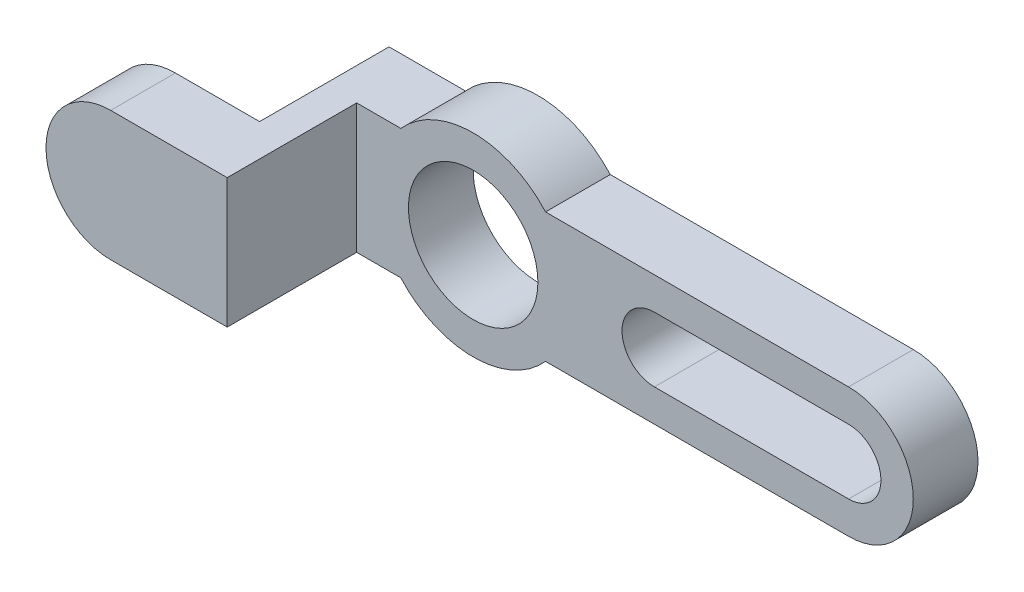
SolidWorks part; units mm, degrees
ref_plane "Front Plane" through (0, 0, 0) normal (0, 0, 1) x (1, 0, 0)
ref_plane "Top Plane" through (0, 0, 0) normal (0, 1, 0) x (1, 0, 0)
ref_plane "Right Plane" through (0, 0, 0) normal (1, 0, 0) x (0, 0, -1)
sketch "Sketch1" plane through (0, 0, 0) normal (0, 0, 1) x (1, 0, 0)
  line L0 (7.0995, 6.35) -> (31.75, 6.35)
  line L1 (-31.75, 6.35) -> (-7.0995, 6.35) construction
  line L2 (-31.75, 6.35) -> (-31.75, -6.35) construction
  line L3 (-31.75, -6.35) -> (-7.0995, -6.35) construction
  line L4 (31.75, 6.35) -> (31.75, -6.35) construction
  line L5 (-31.75, 6.35) -> (31.75, -6.35) construction
  line L6 (-31.75, -6.35) -> (31.75, 6.35) construction
  line L10 (7.0995, -6.35) -> (31.75, -6.35)
  line L14 (-17.78, 6.35) -> (-17.78, -6.35)
  line L15 (-17.78, 6.35) -> (-7.0995, 6.35)
  line L16 (-17.78, -6.35) -> (-7.0995, -6.35)
  line L17 (36.83, 6.35) -> (36.83, -6.35)
  line L18 (31.75, 6.35) -> (36.83, 6.35)
  line L19 (36.83, -6.35) -> (31.75, -6.35)
  arc A1 (-7.0995, -6.35) -> (7.0995, -6.35) centre (0, 0) ccw
  arc A5 (7.0995, 6.35) -> (-7.0995, 6.35) centre (0, 0) ccw
  circle A6 centre (0, 0) radius 6.35
  dimension "D3" = 19.05
  dimension "D4" = 12.7
  dimension "D1" = 63.5
  dimension "D2" = 12.7
  dimension "D5" = 13.97
  dimension "D6" = 36.83
extrude "Boss-Extrude1" add sketch "Sketch1" along normal mid plane 6.35
sketch "Sketch2" plane through (0, 0, -3.175) normal (0, 0, -1) x (-1, 0, 0)
  line L1 (-36.83, -6.35) -> (-36.83, 6.35) construction
  circle A0 centre (-36.83, 0) radius 6.35
  circle A1 centre (-36.83, 0) radius 3.175
  point P5 (-36.83, 0)
  dimension "D1" = 6.35
  dimension "D2" = 3.175
extrude "Boss-Extrude2" add sketch "Sketch2" against normal up to surface (6.35 mm away) up to face at (4.7625, 0, 3.175)
sketch "Sketch4" plane through (0, 0, 3.175) normal (0, 0, 1) x (1, 0, 0)
  line L1 (36.83, 3.175) -> (17.78, 3.175)
  line L2 (36.83, -3.175) -> (17.78, -3.175)
  arc A1 (36.83, -3.175) -> (36.83, 3.175) centre (36.83, 0) ccw construction
  arc A2 (36.83, -3.175) -> (36.83, 3.175) centre (36.83, 0) ccw construction
  arc A3 (36.83, -3.175) -> (36.83, 3.175) centre (36.83, 0) ccw
  arc A4 (17.78, 3.175) -> (17.78, -3.175) centre (17.78, 0) ccw
  arc A5 (17.78, -3.175) -> (17.78, 3.175) centre (17.78, 0) ccw construction
  arc A6 (36.83, 3.175) -> (36.83, -3.175) centre (36.83, 0) ccw construction
  dimension "D1" = 19.05
extrude "Cut-Extrude2" cut sketch "Sketch4" against normal up to surface (6.35 mm away)
sketch "Sketch5" plane through (0, 0, 3.175) normal (0, 0, 1) x (1, 0, 0)
  line L1 (-17.78, 6.35) -> (-11.43, 6.35)
  line L2 (-17.78, 6.35) -> (-17.78, -6.35)
  line L3 (-17.78, -6.35) -> (-11.43, -6.35)
  line L4 (-11.43, 6.35) -> (-11.43, -6.35)
  dimension "D1" = 6.35
extrude "Boss-Extrude3" add sketch "Sketch5" along normal blind 12.7
sketch "Sketch6" plane through (-17.78, 0, 0) normal (-1, 0, 0) x (0, 0, 1)
  line L0 (15.875, -6.35) -> (-3.175, -6.35) construction
  line L1 (15.875, 6.35) -> (9.525, 6.35)
  line L2 (15.875, 6.35) -> (15.875, -6.35)
  line L3 (15.875, -6.35) -> (9.525, -6.35)
  line L4 (9.525, 6.35) -> (9.525, -6.35)
  dimension "D1" = 6.35
extrude "Boss-Extrude4" add sketch "Sketch6" along normal blind 5.08
sketch "Sketch7" plane through (0, 0, 15.875) normal (0, 0, 1) x (1, 0, 0)
  line L0 (-22.86, -6.35) -> (-22.86, 6.35) construction
  line L2 (-22.86, -6.35) -> (-11.43, -6.35) construction
  circle A1 centre (-22.86, 0) radius 6.35
extrude "Boss-Extrude5" add sketch "Sketch7" against normal up to surface (6.35 mm away) up to face at (-20.32, 0, 9.525)
ref_plane "Midplane for Mates" through (0, 0, 12.7) normal (0, 0, 1) x (1, 0, 0)
sketch "Sketch9" plane through (-17.78, 0, 0) normal (-1, 0, 0) x (0, 0, 1)
  line L5 (9.525, -6.35) -> (9.525, 6.35)
  line L6 (9.525, 6.35) -> (-3.175, 6.35)
  line L7 (-3.175, 6.35) -> (-3.175, -6.35)
  line L8 (-3.175, -6.35) -> (9.525, -6.35)
  line L10 (9.525, -6.35) -> (9.525, 6.35)
  line L11 (9.525, 6.35) -> (-3.175, 6.35)
  line L12 (-3.175, 6.35) -> (-3.175, -6.35)
  line L13 (-3.175, -6.35) -> (9.525, -6.35)
  dimension "D1" = 0
extrude "Cut-Extrude4" cut sketch "Sketch9" against normal offset from surface (3.175 mm away) 3.175 up to face at (-11.43, 0, 9.525)
sketch "Sketch10" plane through (0, 0, 15.875) normal (0, 0, 1) x (1, 0, 0)
  line L0 (-29.21, 0) -> (17.78, 0)
  arc A0 (-22.86, 6.35) -> (-22.86, -6.35) centre (-22.86, 0) ccw construction
  dimension "D1" = 46.99
